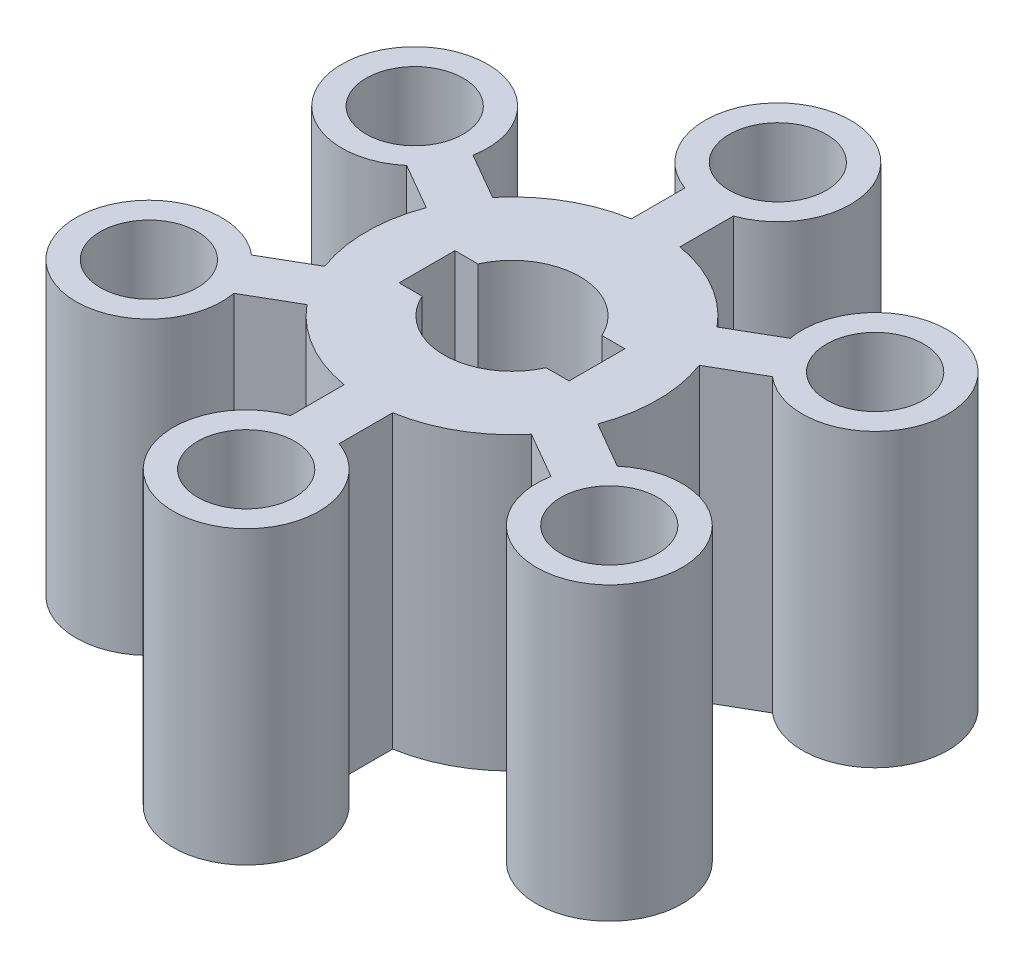
SolidWorks part; units mm, degrees
ref_plane "Front Plane" through (0, 0, 0) normal (0, 0, 1) x (1, 0, 0)
ref_plane "Top Plane" through (0, 0, 0) normal (0, 1, 0) x (1, 0, 0)
ref_plane "Right Plane" through (0, 0, 0) normal (1, 0, 0) x (0, 0, -1)
sketch "Sketch1" plane through (0, 0, 0) normal (0, 1, 0) x (1, 0, 0)
  line L0 (0, 0) -> (0, 50000) construction
  line L1 (-10, 81.2157) -> (-10, 59.1608)
  line L2 (10, 59.1608) -> (10, 81.2157)
  line L3 (65.3349, 49.2681) -> (46.2348, 38.2407)
  line L4 (56.2348, 20.9201) -> (75.3349, 31.9476)
  line L5 (75.3349, -31.9476) -> (56.2348, -20.9201)
  line L6 (46.2348, -38.2407) -> (65.3349, -49.2681)
  line L7 (10, -81.2157) -> (10, -59.1608)
  line L8 (-10, -59.1608) -> (-10, -81.2157)
  line L9 (-65.3349, -49.2681) -> (-46.2348, -38.2407)
  line L10 (-56.2348, -20.9201) -> (-75.3349, -31.9476)
  line L11 (-75.3349, 31.9476) -> (-56.2348, 20.9201)
  line L12 (-46.2348, 38.2407) -> (-65.3349, 49.2681)
  line L13 (0, 0) -> (50000, 0) construction
  line L14 (-35, 11.5) -> (-35, -11.5)
  line L15 (-35, 11.5) -> (-25.5294, 11.5)
  line L16 (-35, -11.5) -> (-25.5294, -11.5)
  line L17 (35, -11.5) -> (25.5294, -11.5)
  line L18 (35, 11.5) -> (25.5294, 11.5)
  line L19 (35, 11.5) -> (35, -11.5)
  circle A0 centre (0, 0) radius 109.5 construction
  arc A1 (10, 81.2157) -> (-10, 81.2157) centre (0, 109.5) ccw
  circle A2 centre (0, 109.5) radius 20
  arc A3 (-56.2348, 20.9201) -> (-56.2348, -20.9201) centre (0, 0) ccw
  arc A4 (75.3349, 31.9476) -> (65.3349, 49.2681) centre (94.8298, 54.75) ccw
  circle A5 centre (94.8298, 54.75) radius 20
  arc A6 (65.3349, -49.2681) -> (75.3349, -31.9476) centre (94.8298, -54.75) ccw
  circle A7 centre (94.8298, -54.75) radius 20
  arc A8 (-10, -81.2157) -> (10, -81.2157) centre (0, -109.5) ccw
  circle A9 centre (0, -109.5) radius 20
  arc A10 (-75.3349, -31.9476) -> (-65.3349, -49.2681) centre (-94.8298, -54.75) ccw
  circle A11 centre (-94.8298, -54.75) radius 20
  arc A12 (-65.3349, 49.2681) -> (-75.3349, 31.9476) centre (-94.8298, 54.75) ccw
  circle A13 centre (-94.8298, 54.75) radius 20
  arc A14 (-10, 59.1608) -> (-46.2348, 38.2407) centre (0, 0) ccw
  arc A15 (56.2348, -20.9201) -> (56.2348, 20.9201) centre (0, 0) ccw
  arc A16 (46.2348, 38.2407) -> (10, 59.1608) centre (0, 0) ccw
  arc A17 (10, -59.1608) -> (46.2348, -38.2407) centre (0, 0) ccw
  arc A18 (-46.2348, -38.2407) -> (-10, -59.1608) centre (0, 0) ccw
  arc A19 (-25.5294, -11.5) -> (25.5294, -11.5) centre (0, 0) ccw
  arc A20 (25.5294, 11.5) -> (-25.5294, 11.5) centre (0, 0) ccw
  point P45 (0, 0)
  point P48 (-35, 0)
  dimension "D1" = 219
  dimension "D2" = 60
  dimension "D3" = 40
  dimension "D4" = 10
  dimension "D6" = 120
  dimension "D7" = 56
  dimension "D5" = 10
  dimension "D8" = 6
  dimension "D9" = 35
  dimension "D10" = 23
extrude "Boss-Extrude1" add sketch "Sketch1" along normal blind 120
